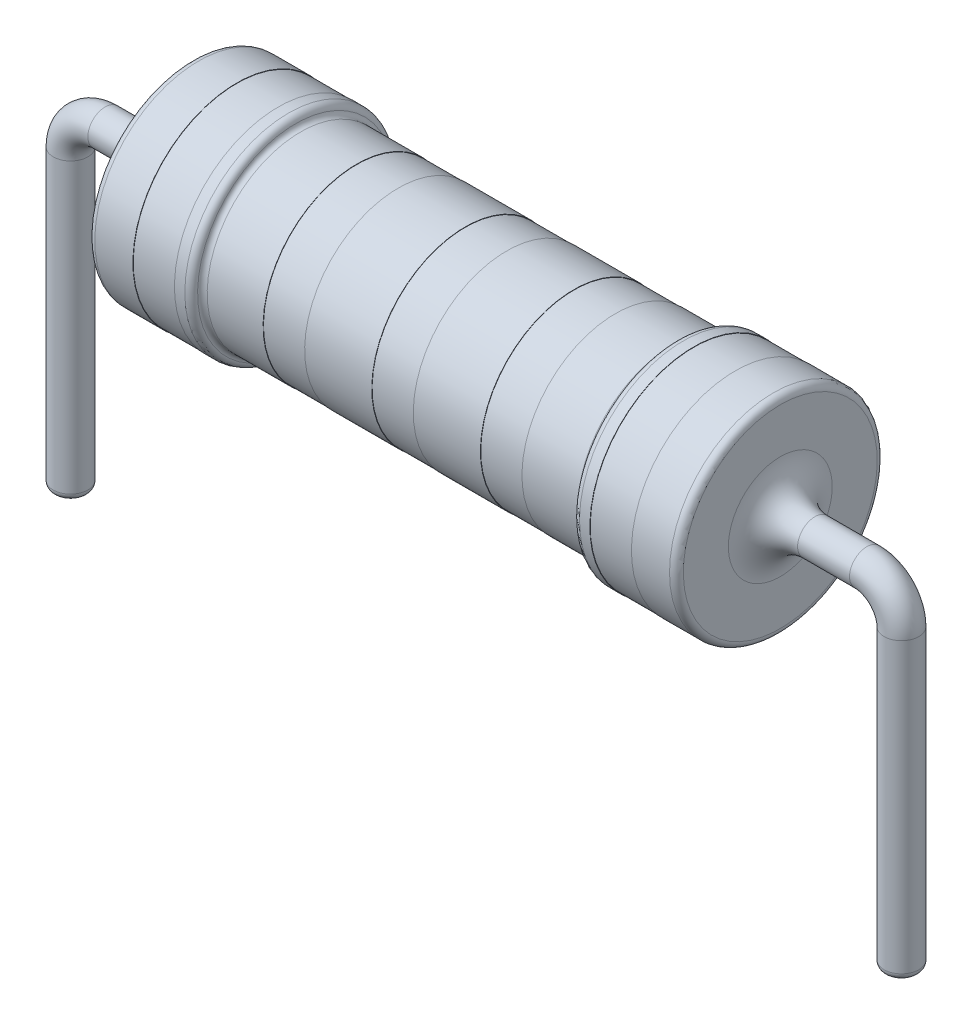
SolidWorks part; units mm, degrees
ref_plane "Front Plane" through (0, 0, 0) normal (0, 0, 1) x (1, 0, 0)
ref_plane "Top Plane" through (0, 0, 0) normal (0, 1, 0) x (1, 0, 0)
ref_plane "Right Plane" through (0, 0, 0) normal (1, 0, 0) x (0, 0, -1)
sketch "Sketch1" plane through (0, 0, 0) normal (0, 0, 1) x (1, 0, 0)
  line L0 (-8.5, 0) -> (8.5, 0)
  line L1 (8.5, 0) -> (8.5, -3)
  line L2 (8.5, -3) -> (7.2, -3)
  line L3 (7.2, -3) -> (7.2, -2.99)
  line L4 (7.2, -2.99) -> (6, -2.99)
  line L5 (6, -2.99) -> (6, -3)
  line L6 (6, -3) -> (5.5, -3)
  line L7 (5.5, -3) -> (5.5, -2.7)
  line L8 (5.5, -2.7) -> (3.738, -2.7)
  line L9 (3.738, -2.7) -> (3.738, -2.69)
  line L10 (3.738, -2.69) -> (2.538, -2.69)
  line L11 (2.538, -2.69) -> (2.538, -2.7)
  line L12 (2.538, -2.7) -> (0.6, -2.7)
  line L13 (0.6, -2.7) -> (0.6, -2.69)
  line L14 (0.6, -2.69) -> (-0.6, -2.69)
  line L16 (-0.6, -2.7) -> (-0.6, -2.69)
  line L17 (-2.538, -2.7) -> (-0.6, -2.7)
  line L18 (-2.538, -2.69) -> (-2.538, -2.7)
  line L19 (-3.738, -2.69) -> (-2.538, -2.69)
  line L20 (-3.738, -2.7) -> (-3.738, -2.69)
  line L21 (-5.5, -2.7) -> (-3.738, -2.7)
  line L22 (-5.5, -3) -> (-5.5, -2.7)
  line L23 (-6, -3) -> (-5.5, -3)
  line L24 (-6, -2.99) -> (-6, -3)
  line L25 (-7.2, -2.99) -> (-6, -2.99)
  line L26 (-7.2, -3) -> (-7.2, -2.99)
  line L27 (-8.5, -3) -> (-7.2, -3)
  line L28 (-8.5, 0) -> (-8.5, -3)
  dimension "D2" = 3
  dimension "D3" = 3
  dimension "D4" = 1.3
  dimension "D5" = 1.2
  dimension "D6" = 0.01
  dimension "D7" = 0.3
  dimension "D8" = 1.2
  dimension "D9" = 0.01
  dimension "D10" = 0.01
revolve "Revolve1" add sketch "Sketch1" angle 360 about L0
sketch "Sketch2" plane through (8.5, 0, 0) normal (1, 0, 0) x (0, 0, -1)
  circle A0 centre (0, 0) radius 0.5
sketch3d "3DSketch1"
  line L0 (8.5, 0, 0) -> (11, 0, 0)
  line L1 (12, -1, 0) -> (12, -9.533, 0)
  arc A0 (12, -1, 0) -> (11, 0, 0) centre (11, -1, 0) ccw
  point P6 (12, 0, 0)
  point P8 (11, -1, 1)
  dimension "D2" = 1
  dimension "D1" = 3.5
sweep "Sweep1" add profiles "Sketch2" path "3DSketch1"
mirror "Mirror1" about plane through (0, 0, 0) normal (1, 0, 0) of "Sweep1"
fillet "Fillet1" radius 0.2 4 edges at (5.5, -3, 0) (8.5, -3, 0) (-5.5, -3, 0) (-8.5, -3, 0)
fillet "Fillet2" radius 0.15 2 edges at (-5.5, -2.7, 0) (5.5, -2.7, 0)
fillet "Fillet5" radius 1 2 edges at (8.5, 0.5, 0) (-8.5, -0.5, 0)
fillet "Fillet6" radius 0.2 2 edges at (-12.5, -9.533, 0) (12.5, -9.533, 0)
